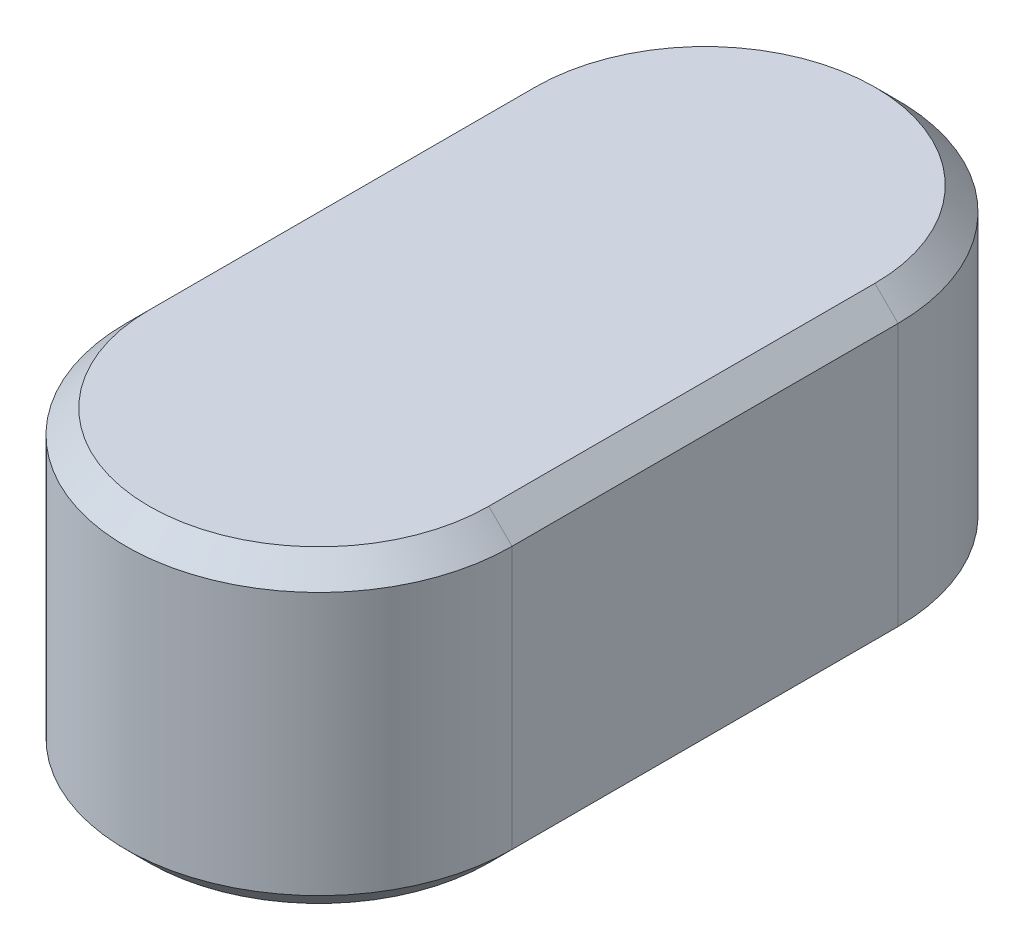
SolidWorks part; units mm, degrees
material "AISI 4340 Steel, normalized"
ref_plane "Front Plane" through (0, 0, 0) normal (0, 0, 1) x (1, 0, 0)
ref_plane "Top Plane" through (0, 0, 0) normal (0, 1, 0) x (1, 0, 0)
ref_plane "Right Plane" through (0, 0, 0) normal (1, 0, 0) x (0, 0, -1)
sketch "Sketch1" plane through (0, 0, 0) normal (0, 1, 0) x (1, 0, 0)
  line L0 (0, 0) -> (0, 10) construction
  line L1 (5, 0) -> (5, 10)
  line L2 (-5, 0) -> (-5, 10)
  arc A0 (5, 0) -> (-5, 0) centre (0, 0) cw
  arc A1 (5, 10) -> (-5, 10) centre (0, 10) ccw
  dimension "D1" = 10
  dimension "D2" = 5
  dimension "D3" = 5
extrude "Boss-Extrude1" add sketch "Sketch1" along normal blind 8
chamfer "Chamfer1" distance 0.6 8 edges at (-5, 0, -5) (0, 0, 5) (0, 0, -15) (5, 0, -5) (-5, 8, -5) (0, 8, 5) (0, 8, -15) (5, 8, -5)
